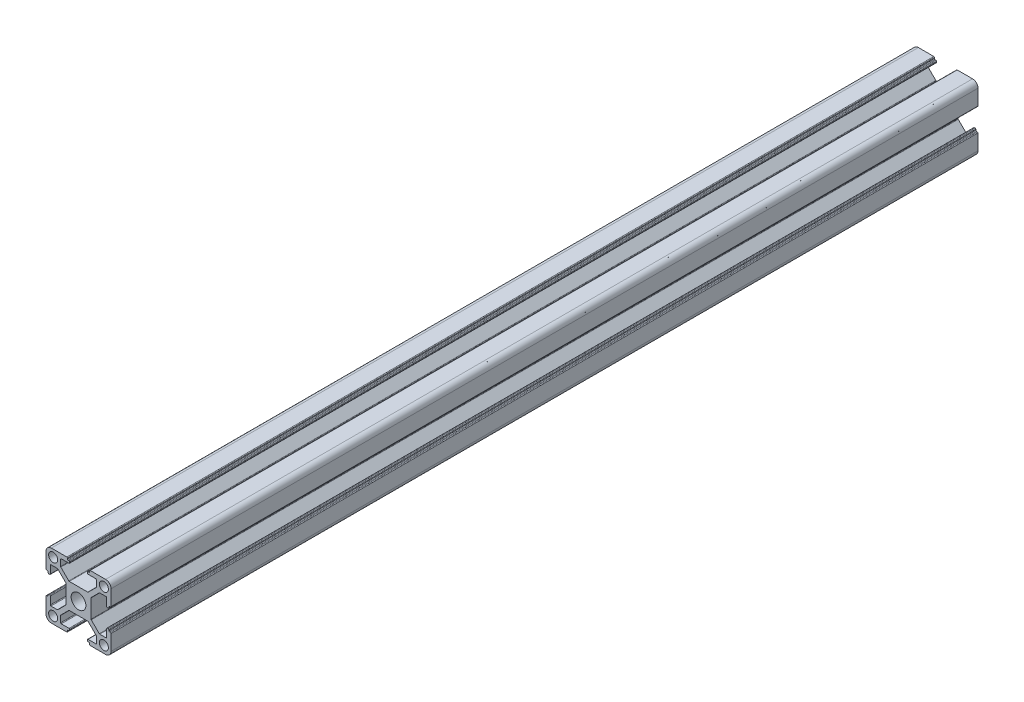
SolidWorks part; units mm, degrees
ref_plane "Alzado" through (0, 0, 0) normal (0, 0, 1) x (1, 0, 0)
ref_plane "Planta" through (0, 0, 0) normal (0, 1, 0) x (1, 0, 0)
ref_plane "Vista lateral" through (0, 0, 0) normal (1, 0, 0) x (0, 0, -1)
ref_plane "Plano1" through (0, 0, -50) normal (0, 0, -1) x (-1, 0, 0)
sketch "Croquis1" plane through (0, 0, -50) normal (0, 0, -1) x (-1, 0, 0)
  line L0 (14.7, -5.1) -> (14.3, -5.1)
  line L1 (14, -4.8) -> (14, -4.4)
  line L2 (13.7, -4.1) -> (13.3, -4.1)
  line L3 (13, -4.4) -> (13, -7.95)
  line L4 (12.7, -8.25) -> (9.7893, -8.25)
  line L5 (9.5772, -8.1622) -> (5.8879, -4.4739)
  line L6 (5.8, -4.2617) -> (5.8, 4.2607)
  line L7 (5.8879, 4.4729) -> (9.5771, 8.1621)
  line L8 (9.7893, 8.25) -> (12.7, 8.25)
  line L9 (13, 7.95) -> (13, 4.4)
  line L10 (13.3, 4.1) -> (13.7, 4.1)
  line L11 (14, 4.4) -> (14, 4.8)
  line L12 (14.3, 5.1) -> (14.7, 5.1)
  line L13 (15, 5.4) -> (15, 12.5)
  line L14 (12.5, 15) -> (5.4, 15)
  line L15 (5.1, 14.7) -> (5.1, 14.3)
  line L16 (4.8, 14) -> (4.4, 14)
  line L17 (4.1, 13.7) -> (4.1, 13.3)
  line L18 (4.4, 13) -> (7.95, 13)
  line L19 (8.25, 12.7) -> (8.25, 9.7883)
  line L20 (8.1621, 9.5761) -> (4.4739, 5.8879)
  line L21 (4.2617, 5.8) -> (-4.2607, 5.8)
  line L22 (-4.4728, 5.8878) -> (-8.1621, 9.5761)
  line L23 (-8.25, 9.7883) -> (-8.25, 12.7)
  line L24 (-7.95, 13) -> (-4.4, 13)
  line L25 (-4.1, 13.3) -> (-4.1, 13.7)
  line L26 (-4.4, 14) -> (-4.8, 14)
  line L27 (-5.1, 14.3) -> (-5.1, 14.7)
  line L28 (-5.4, 15) -> (-12.5, 15)
  line L29 (-15, 12.5) -> (-15, 5.4)
  line L30 (-14.7, 5.1) -> (-14.3, 5.1)
  line L31 (-14, 4.8) -> (-14, 4.4)
  line L32 (-13.7, 4.1) -> (-13.3, 4.1)
  line L33 (-13, 4.4) -> (-13, 7.95)
  line L34 (-12.7, 8.25) -> (-9.7883, 8.25)
  line L35 (-9.5761, 8.1621) -> (-5.8878, 4.4728)
  line L36 (-5.8, 4.2607) -> (-5.8, -4.2617)
  line L37 (-5.8879, -4.4739) -> (-9.5761, -8.1621)
  line L38 (-9.7883, -8.25) -> (-12.7, -8.25)
  line L39 (-13, -7.95) -> (-13, -4.4)
  line L40 (-13.3, -4.1) -> (-13.7, -4.1)
  line L41 (-14, -4.4) -> (-14, -4.8)
  line L42 (-14.3, -5.1) -> (-14.7, -5.1)
  line L43 (-15, -5.4) -> (-15, -12.5)
  line L44 (-12.5, -15) -> (-5.4, -15)
  line L45 (-5.1, -14.7) -> (-5.1, -14.3)
  line L46 (-4.8, -14) -> (-4.4, -14)
  line L47 (-4.1, -13.7) -> (-4.1, -13.3)
  line L48 (-4.4, -13) -> (-7.95, -13)
  line L49 (-8.25, -12.7) -> (-8.25, -9.7893)
  line L50 (-8.1621, -9.5771) -> (-4.4729, -5.8879)
  line L51 (-4.2607, -5.8) -> (4.2617, -5.8)
  line L52 (4.4739, -5.8879) -> (8.1622, -9.5772)
  line L53 (8.25, -9.7893) -> (8.25, -12.7)
  line L54 (7.95, -13) -> (4.4, -13)
  line L55 (4.1, -13.3) -> (4.1, -13.7)
  line L56 (4.4, -14) -> (4.8, -14)
  line L57 (5.1, -14.3) -> (5.1, -14.7)
  line L58 (5.4, -15) -> (12.5, -15)
  line L59 (15, -12.5) -> (15, -5.4)
  arc A0 (15, -5.4) -> (14.7, -5.1) centre (14.7, -5.4) ccw
  arc A1 (14.3, -5.1) -> (14, -4.8) centre (14.3, -4.8) cw
  arc A2 (14, -4.4) -> (13.7, -4.1) centre (13.7, -4.4) ccw
  arc A3 (13.3, -4.1) -> (13, -4.4) centre (13.3, -4.4) ccw
  arc A4 (13, -7.95) -> (12.7, -8.25) centre (12.7, -7.95) cw
  arc A5 (9.7893, -8.25) -> (9.5772, -8.1622) centre (9.7893, -7.95) cw
  arc A6 (5.8879, -4.4739) -> (5.8, -4.2617) centre (6.1, -4.2617) cw
  arc A7 (5.8, 4.2607) -> (5.8879, 4.4729) centre (6.1, 4.2607) cw
  arc A8 (9.5771, 8.1621) -> (9.7893, 8.25) centre (9.7893, 7.95) cw
  arc A9 (12.7, 8.25) -> (13, 7.95) centre (12.7, 7.95) cw
  arc A10 (13, 4.4) -> (13.3, 4.1) centre (13.3, 4.4) ccw
  arc A11 (13.7, 4.1) -> (14, 4.4) centre (13.7, 4.4) ccw
  arc A12 (14, 4.8) -> (14.3, 5.1) centre (14.3, 4.8) cw
  arc A13 (14.7, 5.1) -> (15, 5.4) centre (14.7, 5.4) ccw
  arc A14 (15, 12.5) -> (12.5, 15) centre (12.5, 12.5) ccw
  arc A15 (5.4, 15) -> (5.1, 14.7) centre (5.4, 14.7) ccw
  arc A16 (5.1, 14.3) -> (4.8, 14) centre (4.8, 14.3) cw
  arc A17 (4.4, 14) -> (4.1, 13.7) centre (4.4, 13.7) ccw
  arc A18 (4.1, 13.3) -> (4.4, 13) centre (4.4, 13.3) ccw
  arc A19 (7.95, 13) -> (8.25, 12.7) centre (7.95, 12.7) cw
  arc A20 (8.25, 9.7883) -> (8.1621, 9.5761) centre (7.95, 9.7883) cw
  arc A21 (4.4739, 5.8879) -> (4.2617, 5.8) centre (4.2617, 6.1) cw
  arc A22 (-4.2607, 5.8) -> (-4.4728, 5.8878) centre (-4.2607, 6.1) cw
  arc A23 (-8.1621, 9.5761) -> (-8.25, 9.7883) centre (-7.95, 9.7883) cw
  arc A24 (-8.25, 12.7) -> (-7.95, 13) centre (-7.95, 12.7) cw
  arc A25 (-4.4, 13) -> (-4.1, 13.3) centre (-4.4, 13.3) ccw
  arc A26 (-4.1, 13.7) -> (-4.4, 14) centre (-4.4, 13.7) ccw
  arc A27 (-4.8, 14) -> (-5.1, 14.3) centre (-4.8, 14.3) cw
  arc A28 (-5.1, 14.7) -> (-5.4, 15) centre (-5.4, 14.7) ccw
  arc A29 (-12.5, 15) -> (-15, 12.5) centre (-12.5, 12.5) ccw
  arc A30 (-15, 5.4) -> (-14.7, 5.1) centre (-14.7, 5.4) ccw
  arc A31 (-14.3, 5.1) -> (-14, 4.8) centre (-14.3, 4.8) cw
  arc A32 (-14, 4.4) -> (-13.7, 4.1) centre (-13.7, 4.4) ccw
  arc A33 (-13.3, 4.1) -> (-13, 4.4) centre (-13.3, 4.4) ccw
  arc A34 (-13, 7.95) -> (-12.7, 8.25) centre (-12.7, 7.95) cw
  arc A35 (-9.7883, 8.25) -> (-9.5761, 8.1621) centre (-9.7883, 7.95) cw
  arc A36 (-5.8878, 4.4728) -> (-5.8, 4.2607) centre (-6.1, 4.2607) cw
  arc A37 (-5.8, -4.2617) -> (-5.8879, -4.4739) centre (-6.1, -4.2617) cw
  arc A38 (-9.5761, -8.1621) -> (-9.7883, -8.25) centre (-9.7883, -7.95) cw
  arc A39 (-12.7, -8.25) -> (-13, -7.95) centre (-12.7, -7.95) cw
  arc A40 (-13, -4.4) -> (-13.3, -4.1) centre (-13.3, -4.4) ccw
  arc A41 (-13.7, -4.1) -> (-14, -4.4) centre (-13.7, -4.4) ccw
  arc A42 (-14, -4.8) -> (-14.3, -5.1) centre (-14.3, -4.8) cw
  arc A43 (-14.7, -5.1) -> (-15, -5.4) centre (-14.7, -5.4) ccw
  arc A44 (-15, -12.5) -> (-12.5, -15) centre (-12.5, -12.5) ccw
  arc A45 (-5.4, -15) -> (-5.1, -14.7) centre (-5.4, -14.7) ccw
  arc A46 (-5.1, -14.3) -> (-4.8, -14) centre (-4.8, -14.3) cw
  arc A47 (-4.4, -14) -> (-4.1, -13.7) centre (-4.4, -13.7) ccw
  arc A48 (-4.1, -13.3) -> (-4.4, -13) centre (-4.4, -13.3) ccw
  arc A49 (-7.95, -13) -> (-8.25, -12.7) centre (-7.95, -12.7) cw
  arc A50 (-8.25, -9.7893) -> (-8.1621, -9.5771) centre (-7.95, -9.7893) cw
  arc A51 (-4.4729, -5.8879) -> (-4.2607, -5.8) centre (-4.2607, -6.1) cw
  arc A52 (4.2617, -5.8) -> (4.4739, -5.8879) centre (4.2617, -6.1) cw
  arc A53 (8.1622, -9.5772) -> (8.25, -9.7893) centre (7.95, -9.7893) cw
  arc A54 (8.25, -12.7) -> (7.95, -13) centre (7.95, -12.7) cw
  arc A55 (4.4, -13) -> (4.1, -13.3) centre (4.4, -13.3) ccw
  arc A56 (4.1, -13.7) -> (4.4, -14) centre (4.4, -13.7) ccw
  arc A57 (4.8, -14) -> (5.1, -14.3) centre (4.8, -14.3) cw
  arc A58 (5.1, -14.7) -> (5.4, -15) centre (5.4, -14.7) ccw
  arc A59 (12.5, -15) -> (15, -12.5) centre (12.5, -12.5) ccw
  circle A60 centre (-11.7, 11.7) radius 2.1
  circle A61 centre (-11.7, -11.7) radius 2.1
  circle A62 centre (0, 0) radius 3.4
  circle A63 centre (11.7, 11.7) radius 2.1
  circle A64 centre (11.7, -11.7) radius 2.1
extrude "Saliente-Extruir1" add sketch "Croquis1" against normal blind 400
